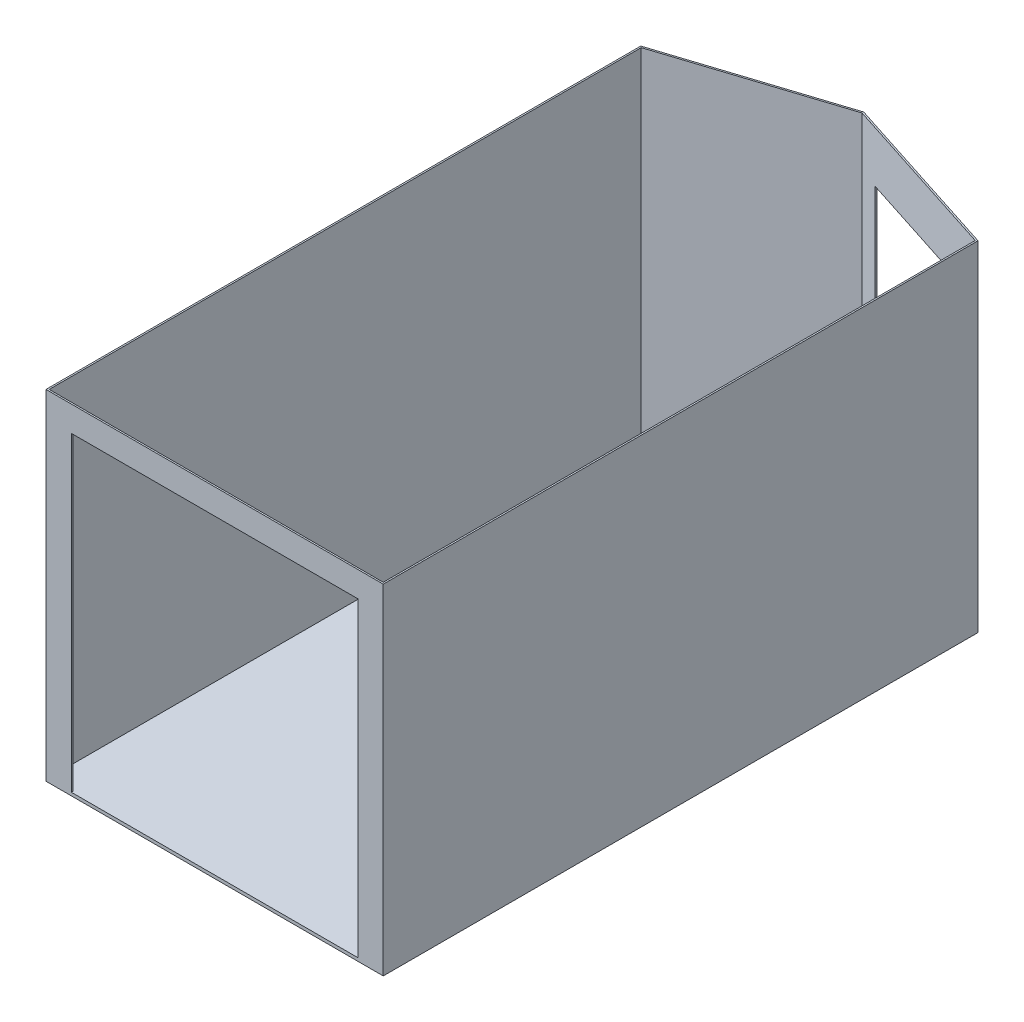
SolidWorks part; units mm, degrees
ref_plane "Front Plane" through (0, 0, 0) normal (0, 0, 1) x (1, 0, 0)
ref_plane "Top Plane" through (0, 0, 0) normal (0, 1, 0) x (1, 0, 0)
ref_plane "Right Plane" through (0, 0, 0) normal (1, 0, 0) x (0, 0, -1)
sketch "Sketch1" plane through (0, 0, 0) normal (0, 1, 0) x (1, 0, 0)
  line L0 (-1003.3, 1778) -> (0, 2101.2892)
  line L1 (1003.3, -1778) -> (-1003.3, -1778)
  line L2 (1003.3, -1778) -> (1003.3, 1778)
  line L3 (1003.3, 1778) -> (-1003.3, 1778) construction
  line L4 (-1003.3, -1778) -> (-1003.3, 1778)
  line L5 (1003.3, -1778) -> (-1003.3, 1778) construction
  line L6 (1003.3, 1778) -> (-1003.3, -1778) construction
  line L7 (0, 2101.2892) -> (1003.3, 1778)
  line L8 (-1012.825, 1784.9381) -> (0, 2111.2965)
  line L9 (0, 2111.2965) -> (1012.825, 1784.9381)
  line L10 (1012.825, -1787.525) -> (1012.825, 1784.9381)
  line L11 (1012.825, -1787.525) -> (-1012.825, -1787.525)
  line L12 (-1012.825, -1787.525) -> (-1012.825, 1784.9381)
  point P0 (0, 0)
  dimension "D1" = 3556
  dimension "D2" = 2006.6
  dimension "D3" = 1054.1
  dimension "D4" = 1054.1
  dimension "D5" = 9.525
extrude "Boss-Extrude1" add sketch "Sketch1" along normal blind 2019.3
sketch "Sketch2" plane through (0, 0, 0) normal (0, -1, 0) x (1, 0, 0)
  line L5 (-1012.825, 1787.525) -> (-1012.825, -1784.9381)
  line L6 (-1012.825, -1784.9381) -> (0, -2111.2965)
  line L7 (0, -2111.2965) -> (1012.825, -1784.9381)
  line L8 (1012.825, -1784.9381) -> (1012.825, 1787.525)
  line L9 (1012.825, 1787.525) -> (-1012.825, 1787.525)
  line L10 (-1012.825, 1787.525) -> (-1012.825, -1784.9381)
  line L11 (-1012.825, -1784.9381) -> (0, -2111.2965)
  line L12 (0, -2111.2965) -> (1012.825, -1784.9381)
  line L13 (1012.825, -1784.9381) -> (1012.825, 1787.525)
  line L14 (1012.825, 1787.525) -> (-1012.825, 1787.525)
  dimension "D1" = 0
extrude "Boss-Extrude2" add sketch "Sketch2" along normal blind 19.05
sketch "Sketch3" plane through (616.322, 0, -1912.7016) normal (0.3067, 0, -0.9518) x (-0.9518, 0, -0.3067)
  line L0 (115.4745, 2019.3) -> (117.4089, 0) construction
  line L1 (-416.5792, 2019.3) -> (647.5281, 2019.3) construction
  line L2 (-409.6411, 0) -> (644.4589, 0) construction
  line L3 (522.1665, 1714.5) -> (-290.6335, 1714.5)
  line L4 (-290.6335, 1714.5) -> (-290.6335, 0)
  line L5 (-290.6335, 0) -> (522.1665, 0)
  line L6 (522.1665, 0) -> (522.1665, 1714.5)
  point P9 (115.7665, 1714.5)
  dimension "D1" = 812.8
  dimension "D2" = 304.8
extrude "Cut-Extrude1" cut sketch "Sketch3" against normal up to next
sketch "Sketch4" plane through (0, 0, 1787.525) normal (0, 0, 1) x (1, 0, 0)
  line L6 (-860.425, 0) -> (860.425, 0)
  line L9 (860.425, -19.05) -> (860.425, 1866.9)
  line L10 (-860.425, 1866.9) -> (-860.425, -19.05)
  line L11 (860.425, 1866.9) -> (-860.425, 1866.9)
  line L12 (860.425, 0) -> (860.425, 1866.9)
  line L13 (-860.425, 1866.9) -> (-860.425, 0)
  line L14 (860.425, 1866.9) -> (-860.425, 1866.9)
  dimension "D1" = 152.4
extrude "Cut-Extrude2" cut sketch "Sketch4" against normal up to next
